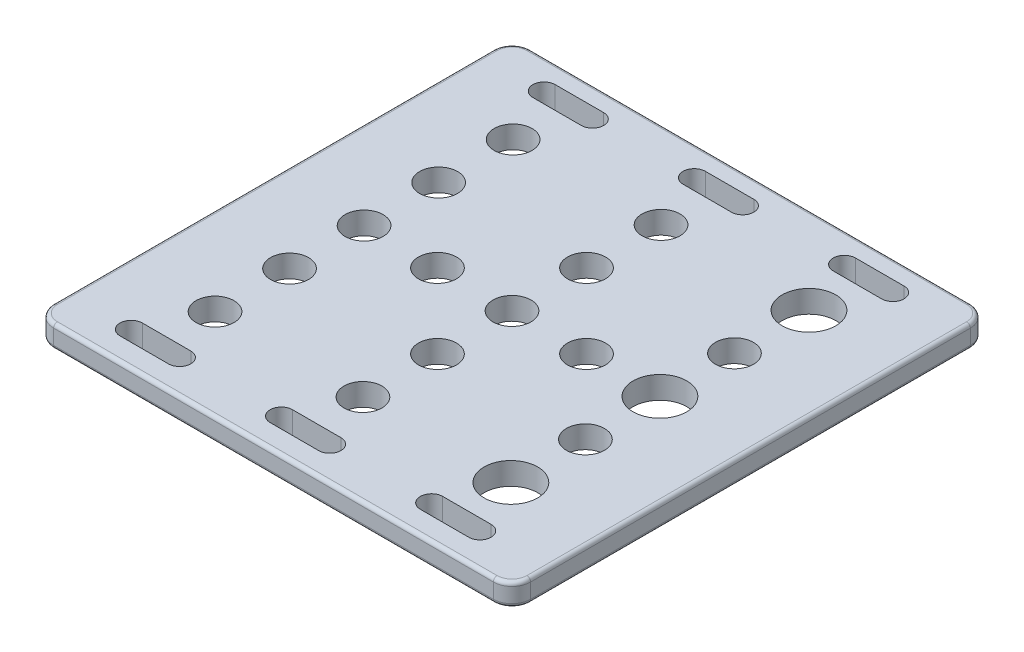
SolidWorks part; units mm, degrees
material "ABS"
ref_plane "Front Plane" through (0, 0, 0) normal (0, 0, 1) x (1, 0, 0)
ref_plane "Top Plane" through (0, 0, 0) normal (0, 1, 0) x (1, 0, 0)
ref_plane "Right Plane" through (0, 0, 0) normal (1, 0, 0) x (0, 0, -1)
sketch "Sketch1" plane through (0, 0, 0) normal (0, 1, 0) x (1, 0, 0)
  line L0 (-20.1, 20.25) -> (23.2, 20.25) construction
  line L1 (-20.1, -19.75) -> (19.6, -19.75) construction
  line L2 (29.5, 32) -> (-29.5, 32)
  line L3 (-32, 29.5) -> (-32, -29.5)
  line L4 (-29.5, -32) -> (29.5, -32)
  line L5 (32, -29.5) -> (32, 29.5)
  line L6 (3, 26.45) -> (-3.5, 26.45)
  line L7 (-23.65, 29.45) -> (-17.15, 29.45)
  line L8 (-17.15, 26.45) -> (-23.65, 26.45)
  line L9 (-3.5, 29.45) -> (3, 29.45)
  line L10 (16.65, 29.45) -> (23.15, 29.45)
  line L11 (23.15, 26.45) -> (16.65, 26.45)
  line L12 (-17.15, -28.95) -> (-23.65, -28.95)
  line L13 (-23.65, -25.95) -> (-17.15, -25.95)
  line L14 (-3.5, -25.95) -> (3, -25.95)
  line L15 (3, -28.95) -> (-3.5, -28.95)
  line L16 (23.15, -28.95) -> (16.65, -28.95)
  line L17 (16.65, -25.95) -> (23.15, -25.95)
  line L18 (-0.25, 0.25) -> (-0.25, -9.75) construction
  arc A0 (-29.5, 32) -> (-32, 29.5) centre (-29.5, 29.5) ccw
  arc A1 (-32, -29.5) -> (-29.5, -32) centre (-29.5, -29.5) ccw
  arc A2 (29.5, -32) -> (32, -29.5) centre (29.5, -29.5) ccw
  arc A3 (32, 29.5) -> (29.5, 32) centre (29.5, 29.5) ccw
  circle A4 centre (-10.25, 0.25) radius 2.55
  circle A5 centre (19.6, 0.25) radius 3.6
  arc A6 (-23.65, 29.45) -> (-23.65, 26.45) centre (-23.65, 27.95) ccw
  arc A7 (-17.15, 26.45) -> (-17.15, 29.45) centre (-17.15, 27.95) ccw
  arc A8 (-3.5, 29.45) -> (-3.5, 26.45) centre (-3.5, 27.95) ccw
  arc A9 (3, 26.45) -> (3, 29.45) centre (3, 27.95) ccw
  arc A10 (23.15, 26.45) -> (23.15, 29.45) centre (23.15, 27.95) ccw
  arc A11 (16.65, 29.45) -> (16.65, 26.45) centre (16.65, 27.95) ccw
  circle A12 centre (19.6, 10.25) radius 2.55
  circle A13 centre (-0.25, 10.25) radius 2.55
  arc A14 (-17.15, -28.95) -> (-17.15, -25.95) centre (-17.15, -27.45) ccw
  arc A15 (-23.65, -25.95) -> (-23.65, -28.95) centre (-23.65, -27.45) ccw
  arc A16 (-3.5, -25.95) -> (-3.5, -28.95) centre (-3.5, -27.45) ccw
  arc A17 (3, -28.95) -> (3, -25.95) centre (3, -27.45) ccw
  arc A18 (23.15, -28.95) -> (23.15, -25.95) centre (23.15, -27.45) ccw
  arc A19 (16.65, -25.95) -> (16.65, -28.95) centre (16.65, -27.45) ccw
  circle A20 centre (19.6, -19.75) radius 3.6
  circle A21 centre (-0.25, -9.75) radius 2.55
  circle A22 centre (19.6, -9.75) radius 2.55
  circle A23 centre (9.75, 0.25) radius 2.55
  circle A24 centre (-0.25, 0.25) radius 2.55
  circle A25 centre (-20.1, -19.75) radius 2.55
  circle A26 centre (-20.1, -9.75) radius 2.55
  circle A27 centre (-20.1, 0.25) radius 2.55
  circle A28 centre (-20.1, 10.25) radius 2.55
  circle A29 centre (19.6, 20.25) radius 3.6
  circle A30 centre (-20.1, 20.25) radius 2.55
  circle A31 centre (-0.25, -19.75) radius 2.55
  circle A32 centre (-0.25, 20.25) radius 2.55
  point P83 (-32, 0)
  point P84 (32, 0)
extrude "Boss-Extrude1" add sketch "Sketch1" along normal blind 3
fillet "Fillet1" radius 0.5 16 edges at (31.2678, 0, 31.2678) (32, 0, 0) (31.2678, 0, -31.2678) (0, 0, -32) (-31.2678, 0, -31.2678) (-32, 0, 0) (-31.2678, 0, 31.2678) (0, 0, 32) (-32, 3, 0) (-31.2678, 3, 31.2678) (-31.2678, 3, -31.2678) (0, 3, -32) (31.2678, 3, -31.2678) (32, 3, 0) (31.2678, 3, 31.2678) (0, 3, 32)
